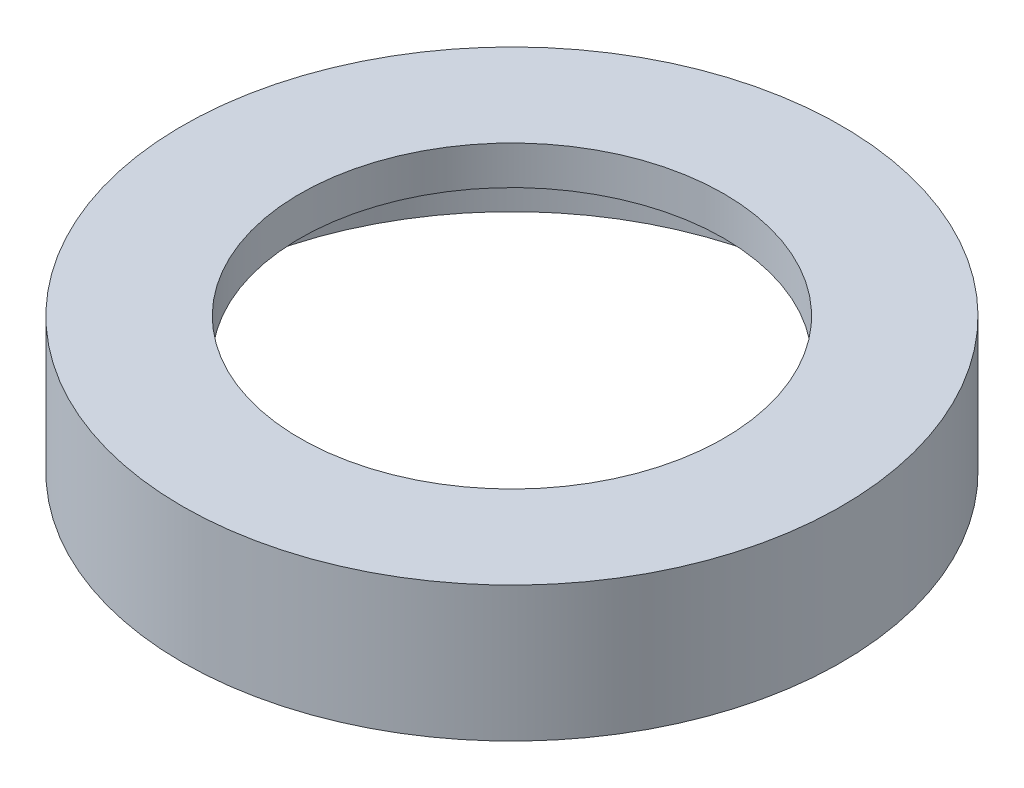
SolidWorks part; units mm, degrees
ref_plane "Alzado" through (0, 0, 0) normal (0, 0, 1) x (1, 0, 0)
ref_plane "Planta" through (0, 0, 0) normal (0, 1, 0) x (1, 0, 0)
ref_plane "Vista lateral" through (0, 0, 0) normal (1, 0, 0) x (0, 0, -1)
sketch "Croquis1" plane through (0, 0, 0) normal (0, 1, 0) x (1, 0, 0)
  circle A0 centre (0, 0) radius 9.0329
  circle A1 centre (0, 0) radius 10.0825
  circle A2 centre (0, 0) radius 17.0749
  circle A3 centre (0, 0) radius 18.3028
  dimension "D1" = 18.0658
  dimension "D2" = 20.165
  dimension "D3" = 34.1499
  dimension "D4" = 36.6055
extrude "Saliente-Extruir2" add sketch "Croquis1" along normal blind 7 contours A2 A1 | A3 A2 | A0
sketch "Croquis3" plane through (0, 7, 0) normal (0, 1, 0) x (1, 0, 0)
  circle A0 centre (0, 0) radius 10.2735
extrude "Cortar-Extruir1" cut sketch "Croquis3" against normal blind 4
sketch "Croquis4" plane through (0, 0, 0) normal (0, 1, 0) x (1, 0, 0)
  circle A0 centre (0, 0) radius 11.2204
  dimension "D1" = 22.4407
extrude "Cortar-Extruir2" cut sketch "Croquis4" along normal blind 2
sketch "Croquis5" plane through (0, 0, 0) normal (0, 1, 0) x (1, 0, 0)
  circle A0 centre (0, 0) radius 10.5468
  dimension "D1" = 21.0935
extrude "Cortar-Extruir4" cut sketch "Croquis5" along normal through all
sketch "Croquis6" plane through (0, 0, 0) normal (0, -1, 0) x (1, 0, 0)
  circle A0 centre (0, 0) radius 16.5236
  circle A1 centre (0, 0) radius 11.2204 construction
  dimension "D1" = 33.0471
extrude "Cortar-Extruir6" cut sketch "Croquis6" against normal blind 6
sketch "Croquis9" plane through (0, 6, 0) normal (0, -1, 0) x (1, 0, 0)
  circle A0 centre (0, 0) radius 10.5468
  circle A1 centre (0, 0) radius 10.9794
  circle A2 centre (0, 0) radius 10.5468 construction
  dimension "D1" = 21.0935
  dimension "D2" = 21.9587
extrude "Cortar-Extruir8" cut sketch "Croquis9" against normal blind 1
sketch "Croquis10" plane through (0, 6, 0) normal (0, -1, 0) x (1, 0, 0)
  circle A0 centre (0, 0) radius 10.9794
  circle A1 centre (0, 0) radius 11.5215
extrude "Saliente-Extruir3" add sketch "Croquis10" along normal blind 1
sketch "Croquis11" plane through (0, 7, 0) normal (0, 1, 0) x (1, 0, 0)
  circle A0 centre (0, 0) radius 16.5909
  circle A1 centre (0, 0) radius 11.7281
  circle A2 centre (0, 0) radius 10.9794 construction
  dimension "D1" = 23.4561
  dimension "D2" = 33.1817
